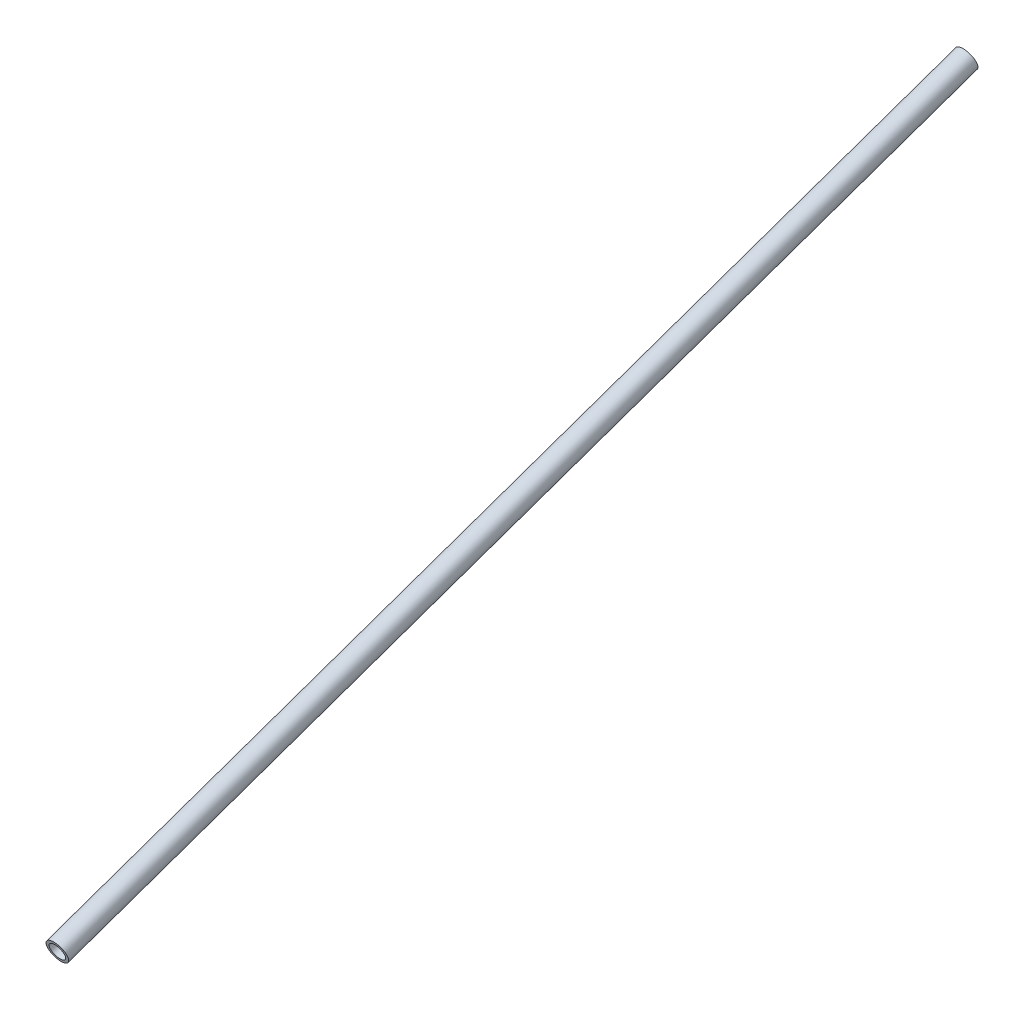
SolidWorks part; units mm, degrees
ref_plane "Front Plane" through (0, 0, 0) normal (0, 0, 1) x (1, 0, 0)
ref_plane "Top Plane" through (0, 0, 0) normal (0, 1, 0) x (1, 0, 0)
ref_plane "Right Plane" through (0, 0, 0) normal (1, 0, 0) x (0, 0, -1)
sketch "reference " plane through (0, 0, 0) normal (1, 0, 0) x (0, 0, -1)
  line L0 (31.4084, 47.1991) -> (665.2022, 269.5975) construction
sketch "Sketch2" plane through (0, 0, 0) normal (1, 0, 0) x (0, 0, -1)
  line L0 (31.4084, 47.1991) -> (834.4306, 328.9798)
  point P3 (834.4306, 328.9798)
  point P4 (0, 0)
other "Pipe standard s40 PIPE 1 SCH 40(1)"
ref_plane "Plane1" through (0, 47.1991, -31.4084) normal (0, 0.3311, -0.9436) x (0, 0.9436, 0.3311)
sketch "Sketch1" plane through (0, 47.1991, -31.4084) normal (0, 0.3311, -0.9436) x (0, 0.9436, 0.3311)
  circle A0 centre (0, 0) radius 6.985
  circle A1 centre (0, 0) radius 9.525
  point P3 (0, 0)
  dimension "D1" = 19.05
  dimension "D2" = 2.54
